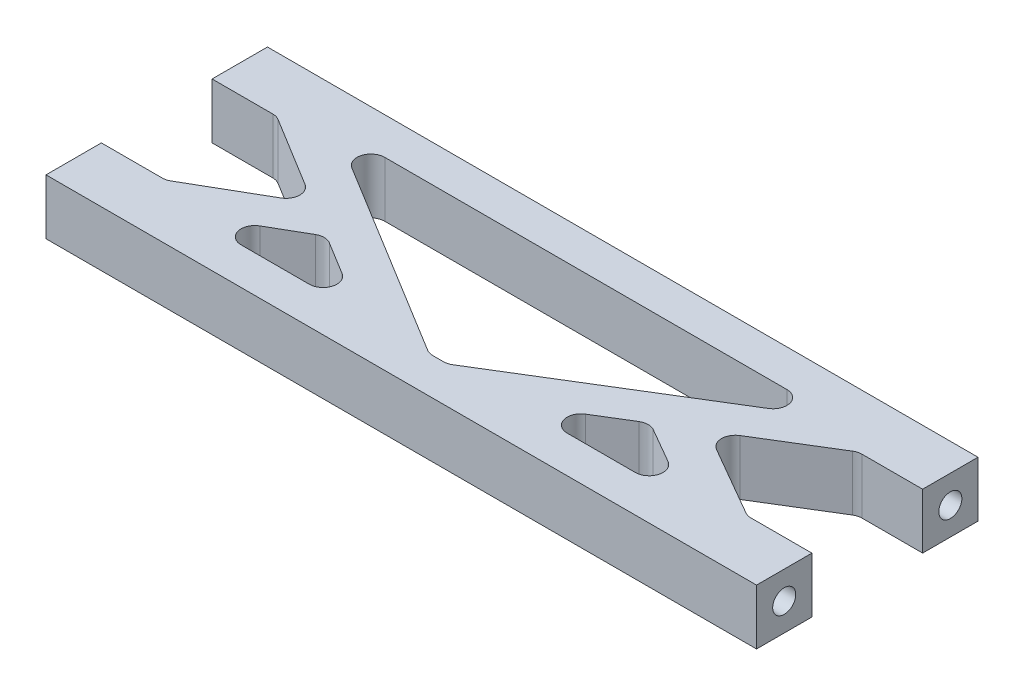
SolidWorks part; units mm, degrees
material "1060 Alloy"
ref_plane "Front Plane" through (0, 0, 0) normal (0, 0, 1) x (1, 0, 0)
ref_plane "Top Plane" through (0, 0, 0) normal (0, 1, 0) x (1, 0, 0)
ref_plane "Right Plane" through (0, 0, 0) normal (1, 0, 0) x (0, 0, -1)
sketch "Sketch1" plane through (0, 0, 0) normal (0, 1, 0) x (1, 0, 0)
  line L1 (0, 0) -> (77, 0)
  line L2 (0, 0) -> (0, 24)
  line L3 (0, 24) -> (77, 24)
  line L4 (77, 0) -> (77, 24)
  dimension "D1" = 24
  dimension "D2" = 77
extrude "Boss-Extrude1" add sketch "Sketch1" along normal blind 6
sketch "Sketch2" plane through (0, 6, 0) normal (0, 1, 0) x (1, 0, 0)
  line L0 (0, 18) -> (7, 18)
  line L2 (0, 24) -> (0, 0) construction
  line L3 (11.3917, 20) -> (65.6083, 20)
  line L4 (7, 6) -> (0, 6)
  line L6 (0, 6) -> (0, 18)
  line L7 (77, 18) -> (70, 18)
  line L8 (77, 0) -> (77, 24) construction
  line L9 (65.6083, 20) -> (39.5, 4)
  line L10 (70, 6) -> (77, 6)
  line L11 (77, 6) -> (77, 18)
  line L12 (39.5, 4) -> (37.5, 4)
  line L13 (37.5, 4) -> (11.3917, 20)
  line L14 (7, 18) -> (17.0825, 11.8211)
  line L15 (17.0825, 11.8211) -> (7, 6)
  line L16 (77, 24) -> (0, 24) construction
  line L17 (0, 0) -> (77, 0) construction
  line L18 (20.9632, 9.4429) -> (11.5359, 4)
  line L19 (11.5359, 4) -> (29.8448, 4)
  line L20 (29.8448, 4) -> (20.9632, 9.4429)
  line L21 (47.1552, 4) -> (56.0368, 9.4429)
  line L22 (56.0368, 9.4429) -> (65.4641, 4)
  line L23 (65.4641, 4) -> (47.1552, 4)
  line L24 (70, 6) -> (59.9175, 11.8211)
  line L25 (59.9175, 11.8211) -> (70, 18)
  dimension "D4" = 4
  dimension "D5" = 4
  dimension "D1" = 6
  dimension "D2" = 6
  dimension "D3" = 4
  dimension "D6" = 4
  dimension "D7" = 4
  dimension "D8" = 4
  dimension "D9" = 2
  dimension "D10" = 30
  dimension "D11" = 7
extrude "Cut-Extrude1" cut sketch "Sketch2" against normal up to next
hole_wizard "Tap Drill for M3 Tap1" positions "Sketch4" profile "Sketch3" hole size "M3" standard "ISO"
sketch "Sketch4" plane through (0, 0, 0) normal (-1, 0, 0) x (0, 0, 1)
  line L0 (-24, 0) -> (-18, 0) construction
  line L1 (-24, 6) -> (-24, 0) construction
  line L2 (0, 6) -> (0, 0) construction
  point P0 (-21, 3)
  point P2 (-3, 3)
  dimension "D1" = 3
  dimension "D2" = 3
  dimension "D3" = 3
sketch "Sketch3" plane through (0, 3, -21) normal (0, 1, 0) x (0, 0, 1)
  line L0 (0, 0) -> (0, 10.7511)
  line L1 (0, 10.7511) -> (1.25, 10)
  line L2 (1.25, 10) -> (1.25, 0)
  line L5 (1.25, 0) -> (0, 0)
  line L10 (0, 10.7511) -> (-1.25, 10) construction
  line L11 (0, -6.35) -> (0, 107.95) construction
  dimension "Hole Dia." = 2.5
  dimension "Hole Depth" = 10
  dimension "Drill Angle" = 118
hole_wizard "Tap Drill for M3 Tap2" positions "Sketch6" profile "Sketch5" hole size "M3" standard "ISO"
sketch "Sketch6" plane through (77, 0, 0) normal (1, 0, 0) x (0, 0, -1)
  line L0 (0, 0) -> (6, 0) construction
  line L1 (0, 6) -> (0, 0) construction
  line L2 (24, 6) -> (24, 0) construction
  point P0 (3, 3)
  point P2 (21, 3)
  dimension "D1" = 3
  dimension "D2" = 3
  dimension "D3" = 3
sketch "Sketch5" plane through (77, 3, -3) normal (0, 1, 0) x (0, 0, -1)
  line L0 (0, 0) -> (0, 10.7511)
  line L1 (0, 10.7511) -> (1.25, 10)
  line L2 (1.25, 10) -> (1.25, 0)
  line L5 (1.25, 0) -> (0, 0)
  line L10 (0, 10.7511) -> (-1.25, 10) construction
  line L11 (0, -6.35) -> (0, 107.95) construction
  dimension "Hole Dia." = 2.5
  dimension "Hole Depth" = 10
  dimension "Drill Angle" = 118
fillet "Fillet1" radius 1.5 16 edges at (47.1552, 3, -4) (56.0368, 3, -9.4429) (70, 3, -6) (59.9175, 3, -11.8211) (70, 3, -18) (65.6083, 3, -20) (39.5, 3, -4) (37.5, 3, -4) (11.3917, 3, -20) (29.8448, 3, -4) (20.9632, 3, -9.4429) (7, 3, -6) (17.0825, 3, -11.8211) (7, 3, -18) (65.4641, 3, -4) (11.5359, 3, -4)
